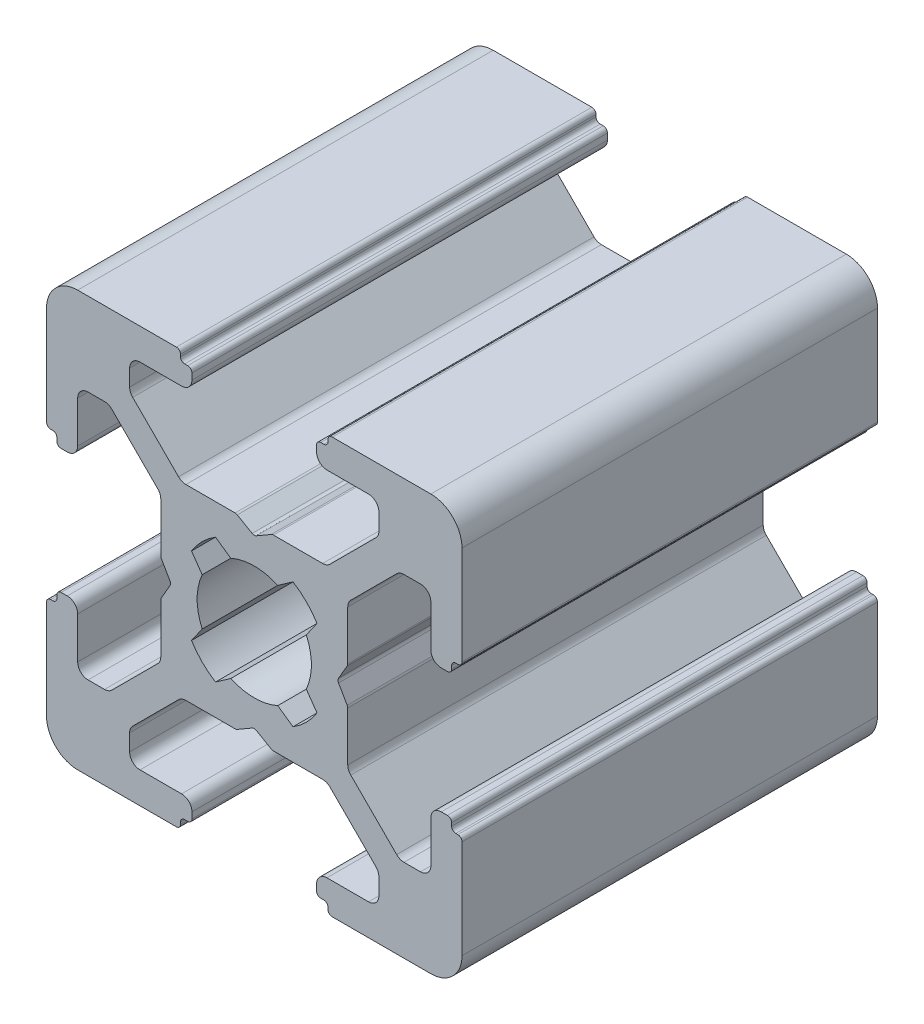
SolidWorks part; units mm, degrees
material "АД31Т ГОСТ 4784-97"
ref_plane "Спереди" through (0, 0, 0) normal (0, 0, 1) x (1, 0, 0)
ref_plane "Сверху" through (0, 0, 0) normal (0, 1, 0) x (1, 0, 0)
ref_plane "Справа" through (0, 0, 0) normal (1, 0, 0) x (0, 0, -1)
sketch "Эскиз1" plane through (0, 0, 0) normal (0, 0, 1) x (1, 0, 0)
  line L0 (3, 9.3) -> (3, 9)
  line L1 (3.35, 9.5) -> (3.2, 9.5)
  line L2 (-3.6454, 4.6464) -> (-5.8536, 6.8546)
  line L3 (-8, 6) -> (-7.2081, 6)
  line L4 (-4.5, 0.9196) -> (-4.5, 3.2919)
  line L5 (3.6454, -4.6464) -> (5.8536, -6.8546)
  line L6 (-9.3, 3) -> (-9, 3)
  line L7 (-9.5, 3.35) -> (-9.5, 3.2)
  line L8 (-9.8, 3.55) -> (-9.7, 3.55)
  line L9 (-10, 8.5) -> (-10, 3.75)
  line L10 (-3.0204, 1.8653) -> (-2.5065, 1.1313)
  line L11 (-8.5, 3.5) -> (-8.5, 5.5)
  line L12 (-3.75, 10) -> (-8.5, 10)
  line L13 (-4.6464, 3.6454) -> (-6.8546, 5.8536)
  line L14 (-0.9196, 4.5) -> (-3.2919, 4.5)
  line L15 (-6, 8) -> (-6, 7.2081)
  line L16 (-4.0577, -0.1) -> (-4.4732, -0.8196)
  line L17 (-4.0577, 0.1) -> (-4.4732, 0.8196)
  line L18 (8, -6) -> (7.2081, -6)
  line L19 (-1.8653, 3.0204) -> (-1.1313, 2.5065)
  line L20 (9.3, -3) -> (9, -3)
  line L22 (1.8653, 3.0204) -> (1.1313, 2.5065)
  line L23 (4.5, -0.9196) -> (4.5, -3.2919)
  line L24 (3.2919, 4.5) -> (0.9196, 4.5)
  line L25 (9.5, -3.35) -> (9.5, -3.2)
  line L26 (3.55, 9.8) -> (3.55, 9.7)
  line L27 (-0.1, 4.0577) -> (-0.8196, 4.4732)
  line L28 (3.0204, 1.8653) -> (2.5065, 1.1313)
  line L29 (3.0204, -1.8653) -> (2.5065, -1.1313)
  line L30 (1.8653, -3.0204) -> (1.1313, -2.5065)
  line L31 (-1.8653, -3.0204) -> (-1.1313, -2.5065)
  line L32 (-3.0204, -1.8653) -> (-2.5065, -1.1313)
  line L33 (0.1, 4.0577) -> (0.8196, 4.4732)
  line L34 (-3.5, 8.5) -> (-5.5, 8.5)
  line L35 (-3.55, 9.8) -> (-3.55, 9.7)
  line L36 (-3.35, 9.5) -> (-3.2, 9.5)
  line L37 (-3, 9.3) -> (-3, 9)
  line L38 (-0.9196, 4.5) -> (-3.2919, 4.5)
  line L39 (3.5, 8.5) -> (5.5, 8.5)
  line L40 (6, 8) -> (6, 7.2081)
  line L41 (4.6464, 3.6454) -> (6.8546, 5.8536)
  line L42 (3.75, 10) -> (8.5, 10)
  line L43 (8.5, 3.5) -> (8.5, 5.5)
  line L44 (10, 8.5) -> (10, 3.75)
  line L45 (9.8, 3.55) -> (9.7, 3.55)
  line L46 (9.5, 3.35) -> (9.5, 3.2)
  line L47 (9.3, 3) -> (9, 3)
  line L48 (8, 6) -> (7.2081, 6)
  line L49 (3.6454, 4.6464) -> (5.8536, 6.8546)
  line L50 (9.8, -3.55) -> (9.7, -3.55)
  line L51 (10, -8.5) -> (10, -3.75)
  line L52 (8.5, -3.5) -> (8.5, -5.5)
  line L53 (3.75, -10) -> (8.5, -10)
  line L54 (4.6464, -3.6454) -> (6.8546, -5.8536)
  line L55 (6, -8) -> (6, -7.2081)
  line L56 (3.5, -8.5) -> (5.5, -8.5)
  line L57 (-0.9196, -4.5) -> (-3.2919, -4.5)
  line L58 (-3, -9.3) -> (-3, -9)
  line L59 (-3.35, -9.5) -> (-3.2, -9.5)
  line L60 (-3.55, -9.8) -> (-3.55, -9.7)
  line L61 (-3.5, -8.5) -> (-5.5, -8.5)
  line L62 (0.1, -4.0577) -> (0.8196, -4.4732)
  line L63 (-3.0204, 1.8653) -> (-2.5065, 1.1313)
  line L64 (-1.8653, 3.0204) -> (-1.1313, 2.5065)
  line L65 (1.8653, 3.0204) -> (1.1313, 2.5065)
  line L66 (3.0204, 1.8653) -> (2.5065, 1.1313)
  line L67 (3.0204, -1.8653) -> (2.5065, -1.1313)
  line L68 (-0.1, -4.0577) -> (-0.8196, -4.4732)
  line L69 (3.55, -9.8) -> (3.55, -9.7)
  line L70 (3.2919, -4.5) -> (0.9196, -4.5)
  line L71 (4.0577, 0.1) -> (4.4732, 0.8196)
  line L72 (1.8653, -3.0204) -> (1.1313, -2.5065)
  line L73 (-1.8653, -3.0204) -> (-1.1313, -2.5065)
  line L74 (-4.0577, -0.1) -> (-4.4732, -0.8196)
  line L75 (-4.0577, 0.1) -> (-4.4732, 0.8196)
  line L76 (-6, -8) -> (-6, -7.2081)
  line L77 (-0.9196, -4.5) -> (-3.2919, -4.5)
  line L78 (-4.6464, -3.6454) -> (-6.8546, -5.8536)
  line L79 (-3.75, -10) -> (-8.5, -10)
  line L80 (-8.5, -3.5) -> (-8.5, -5.5)
  line L81 (-3.0204, -1.8653) -> (-2.5065, -1.1313)
  line L82 (-10, -8.5) -> (-10, -3.75)
  line L83 (-9.8, -3.55) -> (-9.7, -3.55)
  line L84 (-9.5, -3.35) -> (-9.5, -3.2)
  line L85 (-9.3, -3) -> (-9, -3)
  line L86 (-4.5, -0.9196) -> (-4.5, -3.2919)
  line L87 (-8, -6) -> (-7.2081, -6)
  line L88 (-3.6454, -4.6464) -> (-5.8536, -6.8546)
  line L89 (3.35, -9.5) -> (3.2, -9.5)
  line L90 (3, -9.3) -> (3, -9)
  line L91 (4.0577, -0.1) -> (4.4732, -0.8196)
  line L92 (4.0577, 0.1) -> (4.4732, 0.8196)
  line L93 (4.0577, -0.1) -> (4.4732, -0.8196)
  line L94 (4.5, 0.9196) -> (4.5, 3.2919)
  arc A0 (-7.2081, 6) -> (-6.8546, 5.8536) centre (-7.2081, 5.5) cw
  arc A1 (-4.5, 3.2919) -> (-4.6464, 3.6454) centre (-5, 3.2919) ccw
  arc A2 (-6, 7.2081) -> (-5.8536, 6.8546) centre (-5.5, 7.2081) ccw
  arc A3 (-8.5, 10) -> (-10, 8.5) centre (-8.5, 8.5) ccw
  arc A4 (-9.7, 3.55) -> (-9.5, 3.35) centre (-9.7, 3.35) cw
  arc A5 (-10, 3.75) -> (-9.8, 3.55) centre (-9.8, 3.75) ccw
  arc A6 (-9.5, 3.2) -> (-9.3, 3) centre (-9.3, 3.2) ccw
  arc A7 (-9, 3) -> (-8.5, 3.5) centre (-9, 3.5) ccw
  arc A8 (-8, 6) -> (-8.5, 5.5) centre (-8, 5.5) ccw
  arc A9 (-3.2919, 4.5) -> (-3.6454, 4.6464) centre (-3.2919, 5) cw
  arc A10 (-4.4732, -0.8196) -> (-4.5, -0.9196) centre (-4.3, -0.9196) ccw
  arc A11 (-4.4732, 0.8196) -> (-4.5, 0.9196) centre (-4.3, 0.9196) cw
  arc A12 (-4.0577, 0.1) -> (-4.0577, -0.1) centre (-4.2309, 0) cw
  arc A13 (-0.1, 4.0577) -> (0.1, 4.0577) centre (0, 4.2309) ccw
  arc A14 (-3.0204, -1.8653) -> (-1.8653, -3.0204) centre (0, 0) ccw
  arc A15 (-2.5065, 1.1313) -> (-2.5065, -1.1313) centre (0, 0) ccw
  arc A16 (1.1313, 2.5065) -> (-1.1313, 2.5065) centre (0, 0) ccw
  arc A17 (2.5065, -1.1313) -> (2.5065, 1.1313) centre (0, 0) ccw
  arc A18 (-1.1313, -2.5065) -> (1.1313, -2.5065) centre (0, 0) ccw
  arc A19 (-1.8653, 3.0204) -> (-3.0204, 1.8653) centre (0, 0) ccw
  arc A20 (3.0204, 1.8653) -> (1.8653, 3.0204) centre (0, 0) ccw
  arc A21 (1.8653, -3.0204) -> (3.0204, -1.8653) centre (0, 0) ccw
  arc A22 (-0.8196, 4.4732) -> (-0.9196, 4.5) centre (-0.9196, 4.3) ccw
  arc A23 (0.8196, 4.4732) -> (0.9196, 4.5) centre (0.9196, 4.3) cw
  arc A24 (-6, 8) -> (-5.5, 8.5) centre (-5.5, 8) cw
  arc A25 (-3, 9) -> (-3.5, 8.5) centre (-3.5, 9) cw
  arc A26 (-3.2, 9.5) -> (-3, 9.3) centre (-3.2, 9.3) cw
  arc A27 (-3.75, 10) -> (-3.55, 9.8) centre (-3.75, 9.8) cw
  arc A28 (-3.55, 9.7) -> (-3.35, 9.5) centre (-3.35, 9.7) ccw
  arc A29 (3.55, 9.7) -> (3.35, 9.5) centre (3.35, 9.7) cw
  arc A30 (3.75, 10) -> (3.55, 9.8) centre (3.75, 9.8) ccw
  arc A31 (3.2, 9.5) -> (3, 9.3) centre (3.2, 9.3) ccw
  arc A32 (3, 9) -> (3.5, 8.5) centre (3.5, 9) ccw
  arc A33 (6, 8) -> (5.5, 8.5) centre (5.5, 8) ccw
  arc A34 (3.2919, 4.5) -> (3.6454, 4.6464) centre (3.2919, 5) ccw
  arc A35 (8, 6) -> (8.5, 5.5) centre (8, 5.5) cw
  arc A36 (9, 3) -> (8.5, 3.5) centre (9, 3.5) cw
  arc A37 (9.5, 3.2) -> (9.3, 3) centre (9.3, 3.2) cw
  arc A38 (10, 3.75) -> (9.8, 3.55) centre (9.8, 3.75) cw
  arc A39 (9.7, 3.55) -> (9.5, 3.35) centre (9.7, 3.35) ccw
  arc A40 (8.5, 10) -> (10, 8.5) centre (8.5, 8.5) cw
  arc A41 (6, 7.2081) -> (5.8536, 6.8546) centre (5.5, 7.2081) cw
  arc A42 (4.5, 3.2919) -> (4.6464, 3.6454) centre (5, 3.2919) cw
  arc A43 (7.2081, 6) -> (6.8546, 5.8536) centre (7.2081, 5.5) ccw
  arc A44 (7.2081, -6) -> (6.8546, -5.8536) centre (7.2081, -5.5) cw
  arc A45 (4.5, -3.2919) -> (4.6464, -3.6454) centre (5, -3.2919) ccw
  arc A46 (6, -7.2081) -> (5.8536, -6.8546) centre (5.5, -7.2081) ccw
  arc A47 (8.5, -10) -> (10, -8.5) centre (8.5, -8.5) ccw
  arc A48 (9.7, -3.55) -> (9.5, -3.35) centre (9.7, -3.35) cw
  arc A49 (10, -3.75) -> (9.8, -3.55) centre (9.8, -3.75) ccw
  arc A50 (9.5, -3.2) -> (9.3, -3) centre (9.3, -3.2) ccw
  arc A51 (9, -3) -> (8.5, -3.5) centre (9, -3.5) ccw
  arc A52 (8, -6) -> (8.5, -5.5) centre (8, -5.5) ccw
  arc A53 (3.2919, -4.5) -> (3.6454, -4.6464) centre (3.2919, -5) cw
  arc A54 (6, -8) -> (5.5, -8.5) centre (5.5, -8) cw
  arc A55 (3, -9) -> (3.5, -8.5) centre (3.5, -9) cw
  arc A56 (3.2, -9.5) -> (3, -9.3) centre (3.2, -9.3) cw
  arc A57 (3.75, -10) -> (3.55, -9.8) centre (3.75, -9.8) cw
  arc A58 (3.55, -9.7) -> (3.35, -9.5) centre (3.35, -9.7) ccw
  arc A59 (-3.55, -9.7) -> (-3.35, -9.5) centre (-3.35, -9.7) cw
  arc A60 (-3.75, -10) -> (-3.55, -9.8) centre (-3.75, -9.8) ccw
  arc A61 (-3.2, -9.5) -> (-3, -9.3) centre (-3.2, -9.3) ccw
  arc A62 (-3, -9) -> (-3.5, -8.5) centre (-3.5, -9) ccw
  arc A63 (-6, -8) -> (-5.5, -8.5) centre (-5.5, -8) ccw
  arc A64 (0.8196, -4.4732) -> (0.9196, -4.5) centre (0.9196, -4.3) ccw
  arc A65 (-0.8196, -4.4732) -> (-0.9196, -4.5) centre (-0.9196, -4.3) cw
  arc A66 (1.8653, 3.0204) -> (3.0204, 1.8653) centre (0, 0) cw
  arc A67 (3.0204, -1.8653) -> (1.8653, -3.0204) centre (0, 0) cw
  arc A68 (-1.8653, -3.0204) -> (-3.0204, -1.8653) centre (0, 0) cw
  arc A69 (-1.1313, 2.5065) -> (1.1313, 2.5065) centre (0, 0) cw
  arc A70 (1.1313, -2.5065) -> (-1.1313, -2.5065) centre (0, 0) cw
  arc A71 (-3.0204, 1.8653) -> (-1.8653, 3.0204) centre (0, 0) cw
  arc A72 (-0.1, -4.0577) -> (0.1, -4.0577) centre (0, -4.2309) cw
  arc A73 (-4.4732, -0.8196) -> (-4.5, -0.9196) centre (-4.3, -0.9196) ccw
  arc A74 (-4.4732, 0.8196) -> (-4.5, 0.9196) centre (-4.3, 0.9196) cw
  arc A75 (-3.2919, -4.5) -> (-3.6454, -4.6464) centre (-3.2919, -5) ccw
  arc A76 (-8, -6) -> (-8.5, -5.5) centre (-8, -5.5) cw
  arc A77 (-9, -3) -> (-8.5, -3.5) centre (-9, -3.5) cw
  arc A78 (-9.5, -3.2) -> (-9.3, -3) centre (-9.3, -3.2) cw
  arc A79 (-10, -3.75) -> (-9.8, -3.55) centre (-9.8, -3.75) cw
  arc A80 (-9.7, -3.55) -> (-9.5, -3.35) centre (-9.7, -3.35) ccw
  arc A81 (-8.5, -10) -> (-10, -8.5) centre (-8.5, -8.5) cw
  arc A82 (-6, -7.2081) -> (-5.8536, -6.8546) centre (-5.5, -7.2081) cw
  arc A83 (-4.5, -3.2919) -> (-4.6464, -3.6454) centre (-5, -3.2919) cw
  arc A84 (-7.2081, -6) -> (-6.8546, -5.8536) centre (-7.2081, -5.5) ccw
  arc A85 (4.4732, 0.8196) -> (4.5, 0.9196) centre (4.3, 0.9196) ccw
  arc A86 (4.4732, -0.8196) -> (4.5, -0.9196) centre (4.3, -0.9196) cw
  arc A87 (4.0577, 0.1) -> (4.0577, -0.1) centre (4.2309, 0) ccw
  arc A88 (4.4732, 0.8196) -> (4.5, 0.9196) centre (4.3, 0.9196) ccw
  arc A89 (4.4732, -0.8196) -> (4.5, -0.9196) centre (4.3, -0.9196) cw
  point P47 (-4.5, -0.866)
  point P61 (-2.5102, 2.5102)
  point P77 (0.866, 4.5)
  point P231 (0.866, -4.5)
  point P232 (-2.5102, -2.5102)
  point P233 (-4.5, 0.866)
  point P241 (4.5, 0.866)
  point P242 (4.5, -0.866)
extrude "Бобышка-Вытянуть1" add sketch "Эскиз1" along normal blind 20 contours A87 L71 A85 L94 A42 L41 A43 L48 A35 L43 A36 L47 A37 L46 A39 L45 A38 L44 A40 L42 A30 L26 A29 L1 A31 L0 A32 L39 A33 L40 A41 L49 A34 L24 A23 L33 A13 L27 A22 L14 A9 L2 A2 L15 A24 L34 A25 L37 A26 L36 A28
